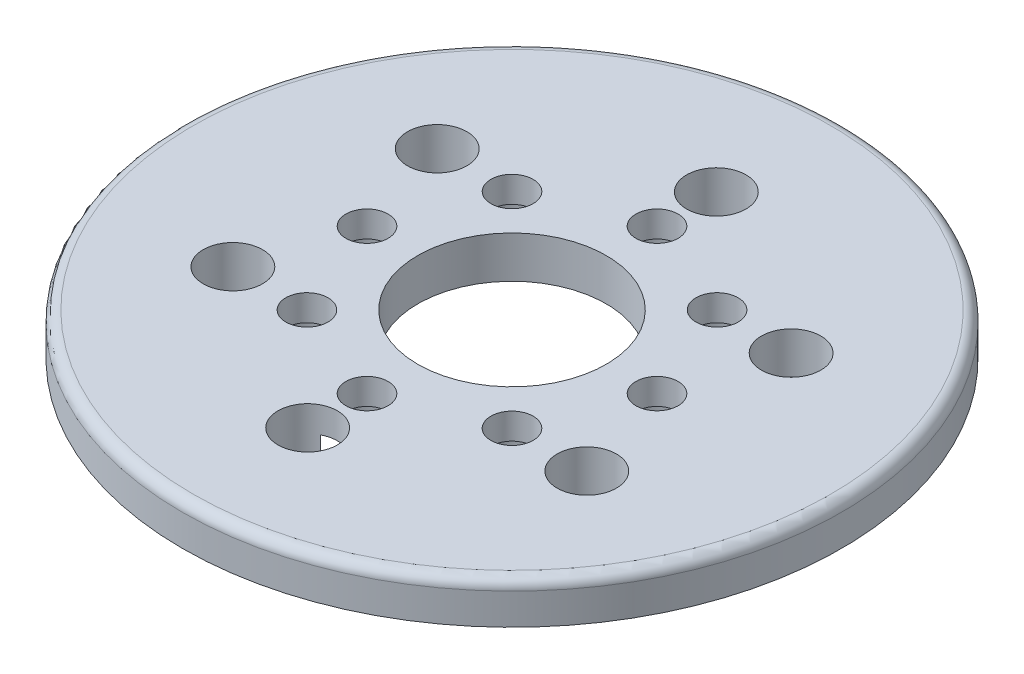
SolidWorks part; units mm, degrees
ref_plane "Front Plane" through (0, 0, 0) normal (0, 0, 1) x (1, 0, 0)
ref_plane "Top Plane" through (0, 0, 0) normal (0, 1, 0) x (1, 0, 0)
ref_plane "Right Plane" through (0, 0, 0) normal (1, 0, 0) x (0, 0, -1)
sketch "Sketch1" plane through (0, 0, 0) normal (0, 1, 0) x (1, 0, 0)
  circle A0 centre (0, 0) radius 25
  circle A1 centre (0, 0) radius 7.15
  dimension "D1" = 14.3
  dimension "D2" = 50
extrude "Boss-Extrude1" add sketch "Sketch1" along normal blind 3.175
sketch "Sketch2" plane through (0, 3.175, 0) normal (0, 1, 0) x (1, 0, 0)
  circle A0 centre (0, 15.5) radius 2.25
  dimension "D2" = 4.5
  dimension "D1" = 15.5
extrude "Cut-Extrude1" cut sketch "Sketch2" against normal through all
pattern_circular "CirPattern1" count 6 over 360 about axis through (0, 0, 0) along (0, 1, 0) of "Cut-Extrude1"
sketch "Sketch4" plane through (0, 0, 0) normal (0, -1, 0) x (1, 0, 0)
  circle A0 centre (0, 11) radius 1.6
  dimension "D2" = 3.2
  dimension "D1" = 11
extrude "Cut-Extrude3" cut sketch "Sketch4" against normal through all
sketch "Sketch5" plane through (0, 0, 0) normal (0, -1, 0) x (1, 0, 0)
  circle A0 centre (0, 11) radius 2.7
  dimension "D1" = 5.4
extrude "Cut-Extrude4" cut sketch "Sketch5" against normal blind 1.2
pattern_circular "CirPattern3" count 8 over 360 about axis through (0, 0, 0) along (0, 1, 0) of "Cut-Extrude3", "Cut-Extrude4"
fillet "Fillet1" radius 0.8 1 edges at (0, 3.175, 25)
